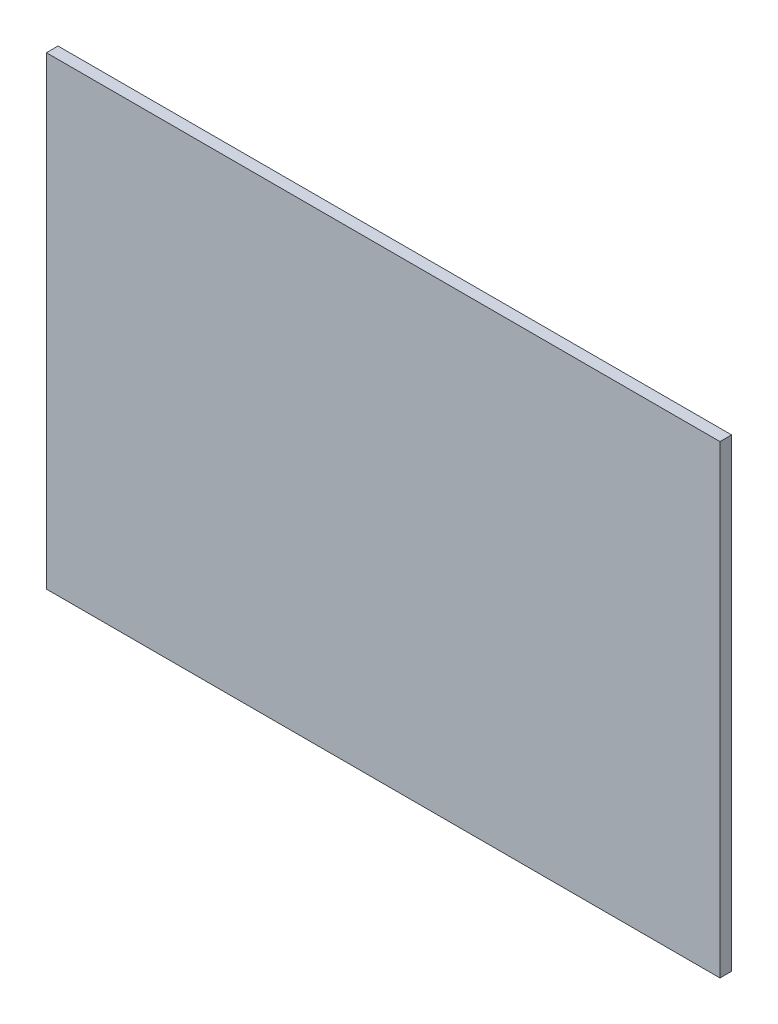
SolidWorks part; units mm, degrees
ref_plane "Front Plane" through (0, 0, 0) normal (0, 0, 1) x (1, 0, 0)
ref_plane "Top Plane" through (0, 0, 0) normal (0, 1, 0) x (1, 0, 0)
ref_plane "Right Plane" through (0, 0, 0) normal (1, 0, 0) x (0, 0, -1)
sketch "Sketch1" plane through (0, 0, 0) normal (0, 0, 1) x (1, 0, 0)
  line L1 (-59.8125, 34.9027) -> (87.5075, 34.9027)
  line L2 (-59.8125, 34.9027) -> (-59.8125, -66.6973)
  line L3 (-59.8125, -66.6973) -> (87.5075, -66.6973)
  line L4 (87.5075, 34.9027) -> (87.5075, -66.6973)
  dimension "D1" = 101.6
  dimension "D2" = 147.32
extrude "Boss-Extrude1" add sketch "Sketch1" along normal blind 2.54
